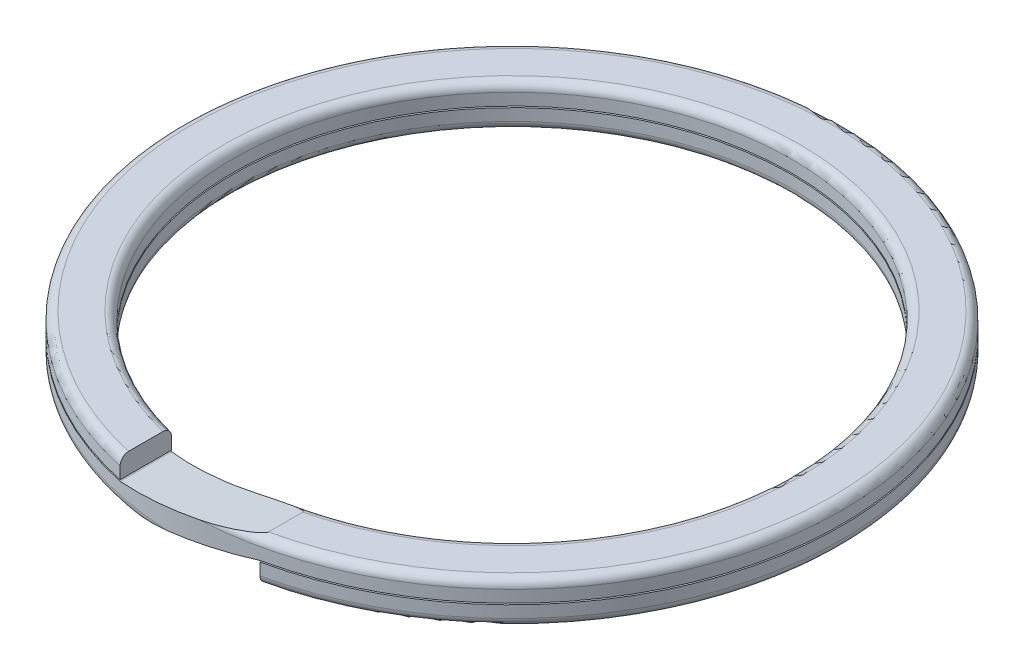
SolidWorks part; units mm, degrees
material "1070"
ref_plane "Front Plane" through (0, 0, 0) normal (0, 0, 1) x (1, 0, 0)
ref_plane "Top Plane" through (0, 0, 0) normal (0, 1, 0) x (1, 0, 0)
ref_plane "Right Plane" through (0, 0, 0) normal (1, 0, 0) x (0, 0, -1)
sketch "Sketch1" plane through (0, 0, 0) normal (0, 0, 1) x (1, 0, 0)
  line L0 (-1.06, 0.32) -> (-1.06, -0.01)
  line L1 (-1.06, -0.01) -> (1.06, 0.32)
  line L2 (1.06, 0.32) -> (-1.06, 0.32)
sketch "Sketch2" plane through (0, 0, 0) normal (0, 0, 1) x (1, 0, 0)
  line L0 (-1.06, -0.32) -> (1.06, -0.32)
  line L1 (1.06, -0.32) -> (1.06, 0.01)
  line L2 (1.06, 0.01) -> (-1.06, -0.32)
sketch "Sketch3" plane through (0, 0, 0) normal (1, 0, 0) x (0, 0, -1)
  line L0 (4.368, -0.32) -> (4.872, -0.32)
  line L1 (5, -0.192) -> (5, 0.192)
  line L2 (4.872, 0.32) -> (4.368, 0.32)
  line L3 (4.24, 0.192) -> (4.24, -0.192)
  line L4 (0, -1) -> (0, 1) construction
  arc A0 (4.24, -0.192) -> (4.368, -0.32) centre (4.368, -0.192) ccw
  arc A1 (4.872, -0.32) -> (5, -0.192) centre (4.872, -0.192) ccw
  arc A2 (5, 0.192) -> (4.872, 0.32) centre (4.872, 0.192) ccw
  arc A3 (4.368, 0.32) -> (4.24, 0.192) centre (4.368, 0.192) ccw
revolve "Revolve1" add sketch "Sketch3" angle 360 about L4
extrude "Cut-Extrude1" cut sketch "Sketch1" along normal blind 8.48
extrude "Cut-Extrude2" cut sketch "Sketch2" along normal blind 8.48
sketch "Sketch4" plane through (0, 0, 0) normal (0, 1, 0) x (1, 0, 0)
  line L0 (-5.544, -5.544) -> (-1.06, -5.544)
  line L1 (-1.06, -5.544) -> (-1.06, -4.002)
  line L2 (1.06, -4.002) -> (1.06, -5.544)
  line L3 (1.06, -5.544) -> (5.544, -5.544)
  line L4 (5.544, -5.544) -> (5.544, 5.544)
  line L5 (5.544, 5.544) -> (-5.544, 5.544)
  line L6 (-5.544, 5.544) -> (-5.544, -5.544)
  arc A0 (-1.06, -4.002) -> (1.06, -4.002) centre (0, 0) ccw
extrude "Cut-Extrude3" cut sketch "Sketch4" along normal blind 0.01 and the other way blind 0.01
other "Freeze***"
